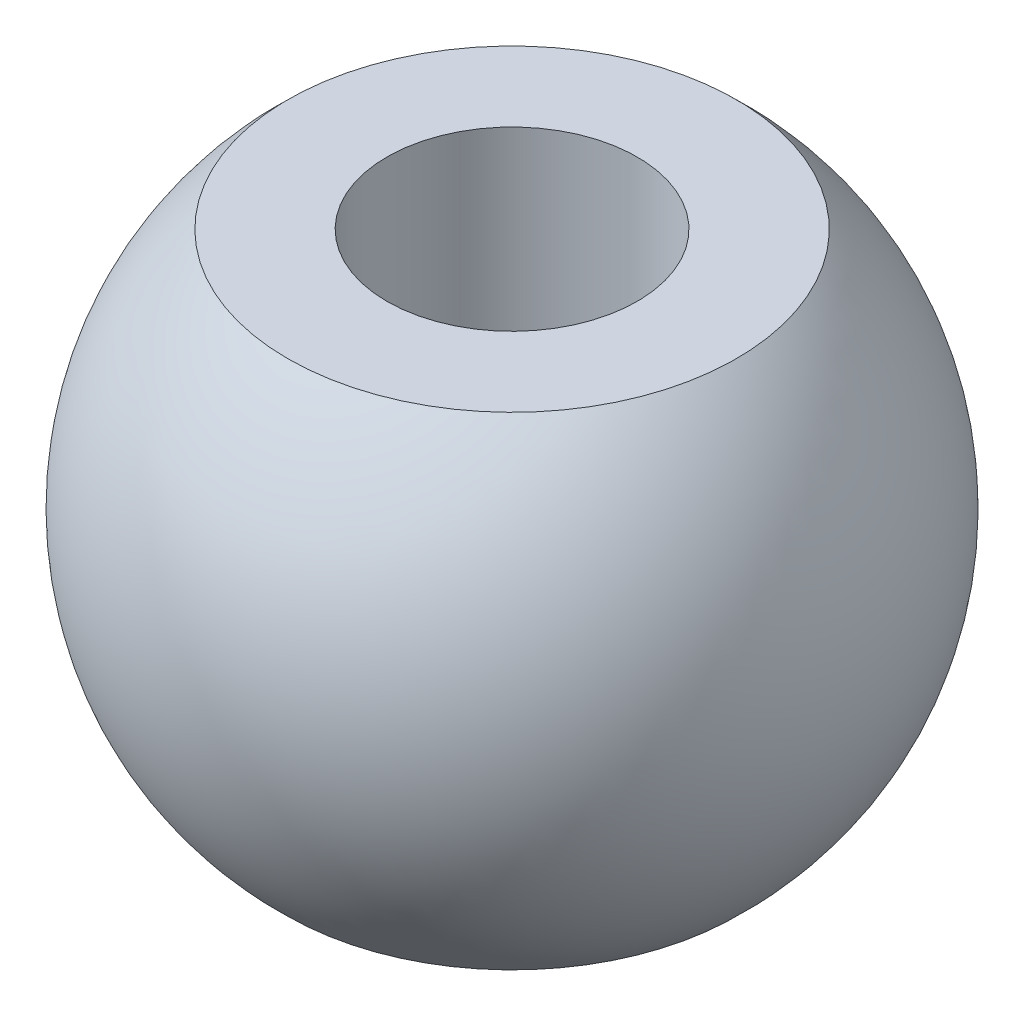
SolidWorks part; units mm, degrees
ref_plane "정면" through (0, 0, 0) normal (0, 0, 1) x (1, 0, 0)
ref_plane "윗면" through (0, 0, 0) normal (0, 1, 0) x (1, 0, 0)
ref_plane "우측면" through (0, 0, 0) normal (1, 0, 0) x (0, 0, -1)
sketch "스케치4" plane through (0, 0, 0) normal (0, 1, 0) x (1, 0, 0)
  line L0 (0, 5.539) -> (0, -5.4421) construction
  line L1 (0, 4.675) -> (0, -4.675)
  arc A0 (0, -4.675) -> (0, 4.675) centre (0, 0) ccw
  dimension "D1" = 9.35
revolve "회전2" add sketch "스케치4" angle 360 about L0
ref_plane "평면2" through (0, 4.675, 0) normal (0, 1, 0) x (1, 0, 0)
sketch "스케치5" plane through (0, 4.675, 0) normal (0, 1, 0) x (1, 0, 0)
  circle A0 centre (0, 0) radius 4.675
extrude "컷-돌출3" cut sketch "스케치5" against normal blind 1.25
mirror "대칭 복사2" about plane through (0, 0, 0) normal (0, 1, 0) of "컷-돌출3"
sketch "스케치6" plane through (0, 3.425, 0) normal (0, 1, 0) x (1, 0, 0)
  circle A0 centre (0, 0) radius 1.775
  dimension "D1" = 3.55
extrude "컷-돌출4" cut sketch "스케치6" against normal through all
sketch "스케치7" plane through (0, -3.425, 0) normal (0, -1, 0) x (1, 0, 0)
  circle A0 centre (0, 0) radius 1.775
